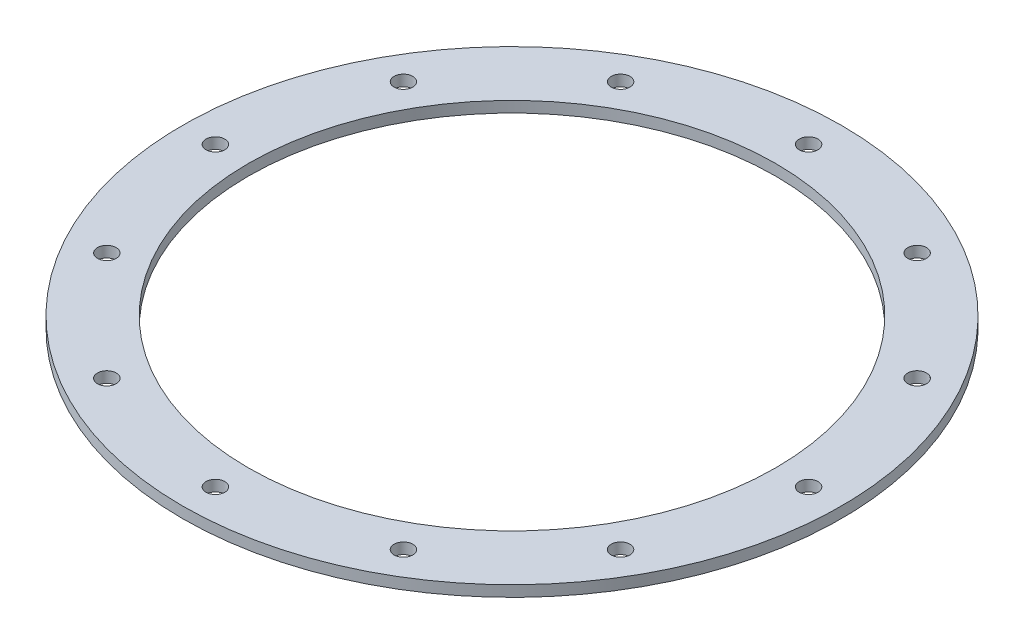
SolidWorks part; units mm, degrees
material "PTFE (general)"
ref_plane "Front Plane" through (0, 0, 0) normal (0, 0, 1) x (1, 0, 0)
ref_plane "Top Plane" through (0, 0, 0) normal (0, 1, 0) x (1, 0, 0)
ref_plane "Right Plane" through (0, 0, 0) normal (1, 0, 0) x (0, 0, -1)
ref_axis "Axis1" through (0, 55, 0) along (0, -1, 0)
sketch "Sketch1" plane through (0, 0, 0) normal (0, 0, 1) x (1, 0, 0)
  line L0 (-38.1, 0) -> (0, 0) construction
  line L1 (-38.1, 0) -> (-47.625, 0)
  line L2 (-38.1, 0) -> (-38.1, 1.5875)
  line L3 (-38.1, 1.5875) -> (-47.625, 1.5875)
  line L4 (-47.625, 0) -> (-47.625, 1.5875)
  line L7 (0, 1.5875) -> (-38.1, 1.5875) construction
  point P12 (-47.625, 0)
  point P18 (-38.1, 1.5875)
revolve "Main" add sketch "Sketch1" angle 360 about axis through (0, 55, 0) along (0, -1, 0)
sketch "Hole Location" plane through (0, 0, 0) normal (0, 1, 0) x (1, 0, 0)
  line L0 (0, 0) -> (-42.8625, 0) construction
  circle A0 centre (0, 0) radius 42.8625 construction
  dimension "D1" = 85.725
hole_wizard "#36 (0.1065) Diameter Hole1" positions "Sketch3" profile "Sketch5" hole size "#36" standard "ANSI Inch" end condition through all
sketch "Sketch3" plane through (0, 0, 0) normal (0, -1, 0) x (-1, 0, 0)
  point P0 (42.8625, 0)
sketch "Sketch5" plane through (-42.8625, 0, 0) normal (1, 0, 0) x (0, 0, -1)
  line L0 (0, 0) -> (0, 1.5875)
  line L1 (0, 1.5875) -> (1.3525, 1.5875)
  line L2 (1.3525, 1.5875) -> (1.3525, 0)
  line L5 (1.3525, 0) -> (0, 0)
  line L11 (0, -6.35) -> (0, 107.95) construction
  dimension "Thru Hole Dia." = 2.7051
  dimension "Thru Hole Depth" = 1.5875
pattern_circular "Screw Passthroughs" count 12 over 360 about axis through (0, 0, 0) along (0, 1, 0) of "#36 (0.1065) Diameter Hole1"
equation "\"D1@Hole Location\"=\"TANK DIAMETER@Cryo Tank.Assembly\"+\"GASKET SEAT THICKNESS@Cryo Tank.Assembly\""
